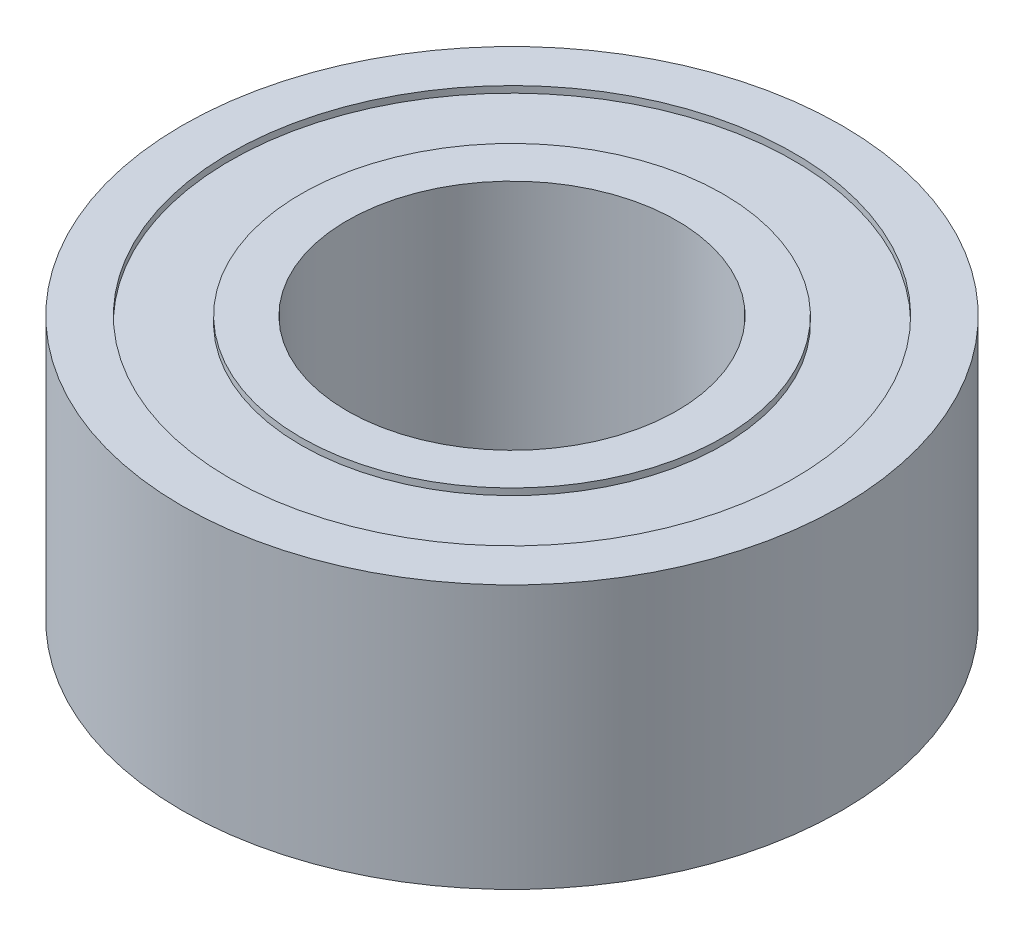
SolidWorks part; units mm, degrees
ref_plane "Front Plane" through (0, 0, 0) normal (0, 0, 1) x (1, 0, 0)
ref_plane "Top Plane" through (0, 0, 0) normal (0, 1, 0) x (1, 0, 0)
ref_plane "Right Plane" through (0, 0, 0) normal (1, 0, 0) x (0, 0, -1)
sketch "Sketch1" plane through (0, 0, 0) normal (0, 1, 0) x (1, 0, 0)
  circle A0 centre (0, 0) radius 5
  circle A1 centre (0, 0) radius 2.5
  dimension "D1" = 10
  dimension "D2" = 5
extrude "Boss-Extrude1" add sketch "Sketch1" along normal blind 4
sketch "Sketch2" plane through (0, 4, 0) normal (0, 1, 0) x (1, 0, 0)
  circle A0 centre (0, 0) radius 3.2
  circle A1 centre (0, 0) radius 4.275
  dimension "D1" = 6.4
  dimension "D2" = 8.55
extrude "Cut-Extrude1" cut sketch "Sketch2" against normal blind 0.1
sketch "Sketch3" plane through (0, 0, 0) normal (0, -1, 0) x (1, 0, 0)
  circle A0 centre (0, 0) radius 3.2 construction
  circle A1 centre (0, 0) radius 4.275
  circle A2 centre (0, 0) radius 4.275
  circle A3 centre (0, 0) radius 3.2
  dimension "D1" = 0
extrude "Cut-Extrude2" cut sketch "Sketch3" against normal blind 0.1
